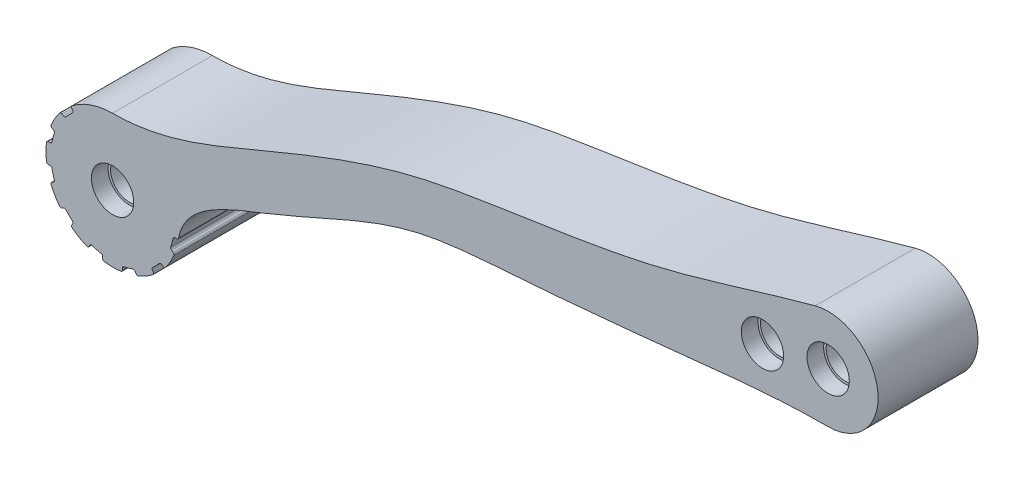
SolidWorks part; units mm, degrees
ref_plane "Alzado" through (0, 0, 0) normal (0, 0, 1) x (1, 0, 0)
ref_plane "Planta" through (0, 0, 0) normal (0, 1, 0) x (1, 0, 0)
ref_plane "Vista lateral" through (0, 0, 0) normal (1, 0, 0) x (0, 0, -1)
sketch "Croquis2" plane through (0, 0, 0) normal (0, 0, 1) x (1, 0, 0)
  line L0 (85.7307, 90.8821) -> (55.8025, 87.4231) construction
  line L1 (55.8025, 87.4231) -> (-37.1797, 50.6223) construction
  line L2 (55.8025, 87.4231) -> (54.5534, 93.2917) construction
  line L5 (55.8025, 87.4231) -> (57.4681, 79.5984) construction
  line L6 (54.5534, 93.2917) -> (57.4681, 79.5984) construction
  line L7 (9.3114, 69.0227) -> (6.5513, 75.9964) construction
  line L8 (9.3114, 69.0227) -> (12.0715, 62.049) construction
  line L9 (-37.1797, 50.6223) -> (-18.5833, 57.9825) construction
  line L11 (176.164, 120.1485) -> (180.0329, 105.656) construction
  line L12 (160.3129, 102.3215) -> (180.0329, 105.656) construction
  line L13 (180.0329, 105.656) -> (180.0329, 90.656) construction
  line L14 (194.8767, 103.497) -> (85.7307, 90.8821) construction
  line L17 (85.7307, 90.8821) -> (86.6492, 82.9351) construction
  line L19 (133.5731, 87.251) -> (130.2386, 106.971) construction
  line L20 (85.7307, 90.8821) -> (84.8121, 98.8292) construction
  line L21 (194.823, 108.1569) -> (107.6301, 93.4132) construction
  line L22 (-37.1797, 50.6223) -> (-32.506, 38.8135) construction
  line L23 (-34.8429, 44.7179) -> (-15.0578, 41.7938) construction
  line L24 (-34.8429, 44.7179) -> (-34.8429, 64.7179) construction
  arc A2 (180.0329, 90.656) -> (176.164, 120.1485) centre (180.0329, 105.656) ccw
  circle A5 centre (160.3129, 102.3215) radius 6.35
  circle A9 centre (180.0329, 105.656) radius 6.35
  circle A13 centre (-34.8429, 44.7179) radius 6.35
  arc A14 (-34.8429, 64.7179) -> (-15.0578, 41.7938) centre (-34.8429, 44.7179) ccw
  spline S0 degree 3 poles (-15.0578, 41.7938) (-13.4229, 52.8557) (19.9319, 63.7267) (50.0674, 80.6719) (92.8603, 83.1479) (133.3882, 87.0917) (164.2759, 90.656) (180.0329, 90.656) knots 0 0 0 0 0.164668 0.401388 0.54424 0.773428 1 1 1 1
  spline S1 degree 3 poles (176.164, 120.1485) (160.6443, 116.0053) (131.1643, 105.6378) (89.9022, 99.6371) (47.5779, 93.1694) (9.2636, 77.1449) (-20.3345, 64.7179) (-34.8429, 64.7179) knots 0 0 0 0 0.21855 0.429652 0.570361 0.803751 1 1 1 1
  dimension "D2" = 8
  dimension "D15" = 12.7
  dimension "D16" = 60
  dimension "D18" = 12.7
  dimension "D19" = 8
  dimension "D11" = 12.7
  dimension "D4" = 195
  dimension "D7" = 100
  dimension "D9" = 15
  dimension "D6" = 40
  dimension "D3" = 140
  dimension "D5" = 20
  dimension "D8" = 8
  dimension "D10" = 6
  dimension "D12" = 7.5
  dimension "D13" = 7.5
  dimension "D14" = 20
extrude "Saliente-Extruir1" add sketch "Croquis2" along normal blind 30
ref_plane "Plano1" through (0, 0, 30) normal (0, 0, 1) x (1, 0, 0)
sketch "Croquis5" plane through (0, 0, 0) normal (0, 0, -1) x (-1, 0, 0)
  circle A0 centre (-180.0329, 105.656) radius 2.5
  circle A1 centre (-180.0329, 105.656) radius 7.4433
  circle A2 centre (-160.3129, 102.3215) radius 2.5
  circle A3 centre (-160.3129, 102.3215) radius 7.335
extrude "Saliente-Extruir4" add sketch "Croquis5" against normal blind 30
sketch "Croquis6" plane through (0, 0, 0) normal (0, 0, -1) x (-1, 0, 0)
  circle A0 centre (-160.3129, 102.3215) radius 6.35
  circle A1 centre (-160.3129, 102.3215) radius 2.5
extrude "Cortar-Extruir2" cut sketch "Croquis6" against normal blind 5 contours A0
sketch "Croquis7" plane through (0, 0, 5) normal (0, 0, -1) x (-1, 0, 0)
  circle A0 centre (-160.3129, 102.3215) radius 5.6
  dimension "D1" = 11.2
extrude "Cortar-Extruir3" cut sketch "Croquis7" against normal blind 30 contours A0
sketch "Croquis8" plane through (0, 0, 30) normal (0, 0, 1) x (1, 0, 0)
  circle A0 centre (160.3129, 102.3215) radius 6.35
  circle A1 centre (160.3129, 102.3215) radius 5.6
  dimension "D1" = 12.7
  dimension "D2" = 11.2
extrude "Cortar-Extruir4" cut sketch "Croquis8" against normal blind 5
sketch "Croquis9" plane through (0, 0, 0) normal (0, 0, -1) x (-1, 0, 0)
  circle A1 centre (-180.0329, 105.656) radius 5.6
  circle A3 centre (-160.3129, 102.3215) radius 5.6 construction
extrude "Cortar-Extruir6" cut sketch "Croquis9" against normal blind 30
sketch "Croquis10" plane through (0, 0, 0) normal (0, 0, -1) x (-1, 0, 0)
  circle A0 centre (-180.0329, 105.656) radius 6.35
  circle A1 centre (-160.3129, 102.3215) radius 6.35 construction
extrude "Cortar-Extruir7" cut sketch "Croquis10" against normal blind 5
sketch "Croquis11" plane through (0, 0, 30) normal (0, 0, 1) x (1, 0, 0)
  circle A0 centre (180.0329, 105.656) radius 6.35
  circle A2 centre (160.3129, 102.3215) radius 6.35 construction
extrude "Cortar-Extruir8" cut sketch "Croquis11" against normal blind 5
sketch "Croquis14" plane through (0, 0, 0) normal (0, 0, -1) x (-1, 0, 0)
  circle A0 centre (34.8429, 44.7179) radius 6.35
  circle A1 centre (34.8429, 44.7179) radius 5.6
  dimension "D1" = 11.2
extrude "Saliente-Extruir5" add sketch "Croquis14" against normal blind 30
sketch "Croquis15" plane through (0, 0, 0) normal (0, 0, -1) x (-1, 0, 0)
  circle A1 centre (34.8429, 44.7179) radius 6.35
  dimension "D1" = 12.7
extrude "Cortar-Extruir9" cut sketch "Croquis15" against normal blind 5
sketch "Croquis16" plane through (0, 0, 30) normal (0, 0, 1) x (1, 0, 0)
  circle A0 centre (-34.8429, 44.7179) radius 6.35
  dimension "D1" = 12.7
extrude "Cortar-Extruir10" cut sketch "Croquis16" against normal blind 5 contours A0
sketch "Croquis17" plane through (0, 0, 0) normal (0, 0, -1) x (-1, 0, 0)
  line L1 (37.8404, 25.4438) -> (37.8429, 25.9619)
  line L2 (31.8453, 25.4438) -> (31.8429, 25.9619)
  line L3 (27.8017, 26.5273) -> (28.0629, 26.9747)
  line L4 (22.6099, 29.5248) -> (22.8668, 29.9747)
  line L5 (19.6498, 32.4849) -> (20.0997, 32.7418)
  line L6 (16.6522, 37.6768) -> (17.0997, 37.938)
  line L7 (15.5688, 41.7204) -> (16.0869, 41.7179)
  line L8 (15.5688, 47.7154) -> (16.0869, 47.7179)
  line L9 (16.6522, 51.759) -> (17.0997, 51.4978)
  line L10 (19.6498, 56.9509) -> (20.0997, 56.694)
  line L11 (22.6099, 59.911) -> (22.8668, 59.4611)
  line L12 (27.8017, 62.9085) -> (28.0629, 62.4611)
  line L13 (31.8453, 63.992) -> (31.8429, 63.4739)
  line L14 (37.8404, 63.992) -> (37.8429, 63.4739)
  line L15 (41.884, 62.9085) -> (41.6228, 62.4611)
  line L16 (47.0758, 59.911) -> (46.8189, 59.4611)
  line L17 (50.036, 56.9509) -> (49.586, 56.694)
  line L18 (53.0335, 51.759) -> (52.586, 51.4978)
  line L19 (54.117, 47.7154) -> (53.5989, 47.7179)
  line L20 (54.117, 41.7204) -> (53.5989, 41.7179)
  line L21 (53.0335, 37.6768) -> (52.586, 37.938)
  line L22 (50.036, 32.4849) -> (49.586, 32.7418)
  line L23 (47.0758, 29.5248) -> (46.8189, 29.9747)
  line L24 (41.884, 26.5273) -> (41.6228, 26.9747)
  line L26 (14.9991, 42.2229) -> (14.8108, 42.1993)
  arc A0 (17.3656, 50.7839) -> (16.6741, 48.2032) centre (34.8429, 44.7179) ccw
  arc A1 (32.3479, 24.8741) -> (37.3378, 24.8741) centre (34.8429, 44.7179) ccw
  arc A2 (37.3378, 24.8741) -> (37.8404, 25.4438) centre (37.2662, 25.4438) ccw
  arc A3 (38.3282, 26.5492) -> (37.8429, 25.9619) centre (38.4408, 25.9619) ccw
  arc A4 (31.3575, 26.5492) -> (31.8429, 25.9619) centre (31.2449, 25.9619) cw
  arc A5 (32.3479, 24.8741) -> (31.8453, 25.4438) centre (32.4195, 25.4438) cw
  arc A6 (22.7603, 28.7802) -> (27.0817, 26.2852) centre (34.8429, 44.7179) ccw
  arc A7 (27.0817, 26.2852) -> (27.8017, 26.5273) centre (27.3045, 26.8144) ccw
  arc A8 (28.7769, 27.2407) -> (28.0629, 26.9747) centre (28.5808, 26.6757) ccw
  arc A9 (22.7603, 28.7802) -> (22.6099, 29.5248) centre (23.1071, 29.2377) cw
  arc A10 (22.7401, 30.726) -> (22.8668, 29.9747) centre (22.3489, 30.2737) cw
  arc A11 (16.4102, 36.9568) -> (18.9051, 32.6353) centre (34.8429, 44.7179) ccw
  arc A12 (18.9051, 32.6353) -> (19.6498, 32.4849) centre (19.3627, 32.9822) ccw
  arc A13 (20.8509, 32.6152) -> (20.0997, 32.7418) centre (20.3987, 32.224) ccw
  arc A14 (16.4102, 36.9568) -> (16.6522, 37.6768) centre (16.9393, 37.1796) cw
  arc A15 (17.3656, 38.6519) -> (17.0997, 37.938) centre (16.8007, 38.4559) cw
  arc A16 (14.9991, 47.2129) -> (14.9991, 42.2229) centre (34.8429, 44.7179) ccw
  arc A17 (14.9991, 42.2229) -> (15.5688, 41.7204) centre (15.5688, 42.2945) ccw
  arc A18 (16.6741, 41.2326) -> (16.0869, 41.7179) centre (16.0869, 41.1199) ccw
  arc A19 (14.9991, 47.2129) -> (15.5688, 47.7154) centre (15.5688, 47.1413) cw
  arc A20 (16.6741, 48.2032) -> (16.0869, 47.7179) centre (16.0869, 48.3159) cw
  arc A21 (18.9051, 56.8005) -> (16.4102, 52.4791) centre (34.8429, 44.7179) ccw
  arc A22 (16.4102, 52.4791) -> (16.6522, 51.759) centre (16.9393, 52.2563) ccw
  arc A23 (17.3656, 50.7839) -> (17.0997, 51.4978) centre (16.8007, 50.98) ccw
  arc A24 (18.9051, 56.8005) -> (19.6498, 56.9509) centre (19.3627, 56.4537) cw
  arc A25 (20.8509, 56.8207) -> (20.0997, 56.694) centre (20.3987, 57.2119) cw
  arc A26 (27.0817, 63.1506) -> (22.7603, 60.6556) centre (34.8429, 44.7179) ccw
  arc A27 (22.7603, 60.6556) -> (22.6099, 59.911) centre (23.1071, 60.1981) ccw
  arc A28 (22.7401, 58.7098) -> (22.8668, 59.4611) centre (22.3489, 59.1621) ccw
  arc A29 (27.0817, 63.1506) -> (27.8017, 62.9085) centre (27.3045, 62.6215) cw
  arc A30 (28.7769, 62.1952) -> (28.0629, 62.4611) centre (28.5808, 62.7601) cw
  arc A31 (37.3378, 64.5617) -> (32.3479, 64.5617) centre (34.8429, 44.7179) ccw
  arc A32 (32.3479, 64.5617) -> (31.8453, 63.992) centre (32.4195, 63.992) ccw
  arc A33 (31.3575, 62.8866) -> (31.8429, 63.4739) centre (31.2449, 63.4739) ccw
  arc A34 (37.3378, 64.5617) -> (37.8404, 63.992) centre (37.2662, 63.992) cw
  arc A35 (38.3282, 62.8866) -> (37.8429, 63.4739) centre (38.4408, 63.4739) cw
  arc A36 (46.9255, 60.6556) -> (42.604, 63.1506) centre (34.8429, 44.7179) ccw
  arc A37 (42.604, 63.1506) -> (41.884, 62.9085) centre (42.3812, 62.6215) ccw
  arc A38 (40.9088, 62.1952) -> (41.6228, 62.4611) centre (41.1049, 62.7601) ccw
  arc A39 (46.9255, 60.6556) -> (47.0758, 59.911) centre (46.5786, 60.1981) cw
  arc A40 (46.9456, 58.7098) -> (46.8189, 59.4611) centre (47.3368, 59.1621) cw
  arc A41 (53.2756, 52.4791) -> (50.7806, 56.8005) centre (34.8429, 44.7179) ccw
  arc A42 (50.7806, 56.8005) -> (50.036, 56.9509) centre (50.323, 56.4537) ccw
  arc A43 (48.8348, 56.8207) -> (49.586, 56.694) centre (49.287, 57.2119) ccw
  arc A44 (53.2756, 52.4791) -> (53.0335, 51.759) centre (52.7464, 52.2563) cw
  arc A45 (52.3201, 50.7839) -> (52.586, 51.4978) centre (52.885, 50.98) cw
  arc A46 (54.6866, 42.2229) -> (54.6866, 47.2129) centre (34.8429, 44.7179) ccw
  arc A47 (54.6866, 47.2129) -> (54.117, 47.7154) centre (54.117, 47.1413) ccw
  arc A48 (53.0116, 48.2032) -> (53.5989, 47.7179) centre (53.5989, 48.3159) ccw
  arc A49 (54.6866, 42.2229) -> (54.117, 41.7204) centre (54.117, 42.2945) cw
  arc A50 (53.0116, 41.2326) -> (53.5989, 41.7179) centre (53.5989, 41.1199) cw
  arc A51 (50.7806, 32.6353) -> (53.2756, 36.9568) centre (34.8429, 44.7179) ccw
  arc A52 (53.2756, 36.9568) -> (53.0335, 37.6768) centre (52.7464, 37.1796) ccw
  arc A53 (52.3201, 38.6519) -> (52.586, 37.938) centre (52.885, 38.4559) ccw
  arc A54 (50.7806, 32.6353) -> (50.036, 32.4849) centre (50.323, 32.9822) cw
  arc A55 (48.8348, 32.6152) -> (49.586, 32.7418) centre (49.287, 32.224) cw
  arc A56 (42.604, 26.2852) -> (46.9255, 28.7802) centre (34.8429, 44.7179) ccw
  arc A57 (46.9255, 28.7802) -> (47.0758, 29.5248) centre (46.5786, 29.2377) ccw
  arc A58 (46.9456, 30.726) -> (46.8189, 29.9747) centre (47.3368, 30.2737) ccw
  arc A59 (42.604, 26.2852) -> (41.884, 26.5273) centre (42.3812, 26.8144) cw
  arc A60 (40.9088, 27.2407) -> (41.6228, 26.9747) centre (41.1049, 26.6757) cw
  arc A61 (22.7401, 58.7098) -> (20.8509, 56.8207) centre (34.8429, 44.7179) ccw
  arc A62 (31.3575, 62.8866) -> (28.7769, 62.1952) centre (34.8429, 44.7179) ccw
  arc A63 (40.9088, 62.1952) -> (38.3282, 62.8866) centre (34.8429, 44.7179) ccw
  arc A64 (48.8348, 56.8207) -> (46.9456, 58.7098) centre (34.8429, 44.7179) ccw
  arc A65 (53.0116, 48.2032) -> (52.3201, 50.7839) centre (34.8429, 44.7179) ccw
  arc A66 (52.3201, 38.6519) -> (53.0116, 41.2326) centre (34.8429, 44.7179) ccw
  arc A67 (46.9456, 30.726) -> (48.8348, 32.6152) centre (34.8429, 44.7179) ccw
  arc A68 (38.3282, 26.5492) -> (40.9088, 27.2407) centre (34.8429, 44.7179) ccw
  arc A69 (28.7769, 27.2407) -> (31.3575, 26.5492) centre (34.8429, 44.7179) ccw
  arc A70 (20.8509, 32.6152) -> (22.7401, 30.726) centre (34.8429, 44.7179) ccw
  arc A71 (16.6741, 41.2326) -> (17.3656, 38.6519) centre (34.8429, 44.7179) ccw
  circle A72 centre (34.8429, 44.7179) radius 20
  spline S0 degree 1 poles (15.5688, 41.7204) (15.181, 41.7086) knots 0 0 1 1
  dimension "D1" = 12
extrude "Cortar-Extruir11" cut sketch "Croquis17" against normal blind 30
sketch "Croquis19" plane through (0, 0, 0) normal (0, 0, -1) x (-1, 0, 0)
  line L1 (14.6166, 43.2019) -> (14.8095, 41.6457)
  line L2 (14.8095, 41.6457) -> (15.218, 41.5713)
  line L3 (15.218, 41.5713) -> (15.5688, 41.7204)
  line L4 (15.5688, 41.7204) -> (15.218, 41.5713)
  arc A0 (14.9991, 42.2229) -> (15.5688, 41.7204) centre (15.595, 42.3243) ccw
  spline S0 degree 3 poles (14.9991, 42.2229) (14.8871, 42.5551) (14.7539, 42.8796) (14.6166, 43.2019) knots 0 0 0 0 1 1 1 1
extrude "Cortar-Extruir12" cut sketch "Croquis19" against normal blind 30 contours A0 S0 L1 L2 L3
